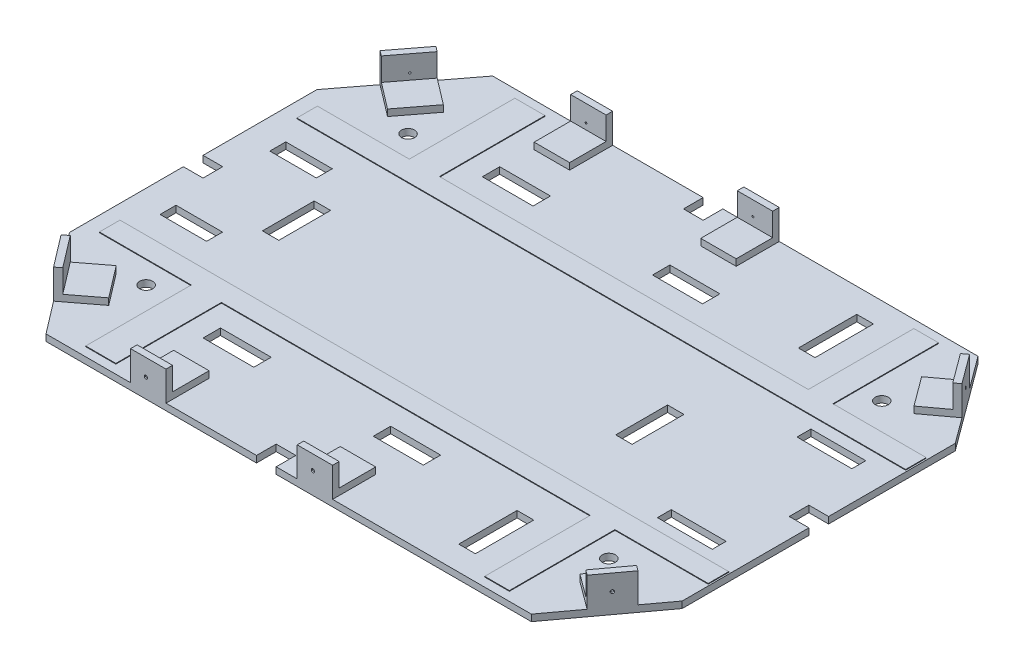
SolidWorks part; units mm, degrees
ref_plane "Front Plane" through (0, 0, 0) normal (0, 0, 1) x (1, 0, 0)
ref_plane "Top Plane" through (0, 0, 0) normal (0, 1, 0) x (1, 0, 0)
ref_plane "Right Plane" through (0, 0, 0) normal (1, 0, 0) x (0, 0, -1)
sketch "Sketch2" plane through (0, 0, 0) normal (0, 1, 0) x (1, 0, 0)
  line L0 (0, -190.295) -> (0, 190.295)
  line L1 (0, 190.295) -> (118.58, 345.4877)
  line L2 (118.58, 345.4877) -> (863.58, 345.4877)
  line L3 (863.58, 345.4877) -> (963.71, 209.8289)
  line L4 (963.71, 209.8289) -> (963.71, -209.8289)
  line L5 (-252.0448, 0) -> (1397.8872, 0) construction
  line L6 (863.58, -345.4877) -> (963.71, -209.8289)
  line L7 (118.58, -345.4877) -> (863.58, -345.4877)
  line L8 (0, -190.295) -> (118.58, -345.4877)
  point P10 (963.71, 0)
  point P13 (0, 0)
  dimension "D1" = 745
  dimension "D2" = 380.59
  dimension "D3" = 195.31
  dimension "D4" = 168.61
  dimension "D5" = 118.58
  dimension "D6" = 100.13
extrude "Boss-Extrude1" add sketch "Sketch2" along normal blind 10 contours L2 L3 L4 L6 L7 L8 L0 L1
sketch "Sketch3" plane through (0, 10, 0) normal (0, 1, 0) x (1, 0, 0)
  line L0 (-153.0587, 0) -> (1034.1611, 0) construction
  line L1 (13.2156, 0) -> (983.2156, 0) construction
  line L2 (0, -190.295) -> (0, 190.295) construction
  line L3 (28.177, 166.1961) -> (168.2416, 166.1961)
  line L4 (28.177, 166.1961) -> (28.177, 134.8384)
  line L5 (28.177, 134.8384) -> (956.3666, 134.8384)
  line L6 (956.3666, 166.1961) -> (956.3666, 134.8384)
  line L7 (168.2416, 327.1659) -> (214.233, 327.1659)
  line L8 (168.2416, 327.1659) -> (168.2416, 166.1961)
  line L10 (214.233, 327.1659) -> (214.233, 166.1961)
  line L11 (776.5822, 327.1659) -> (814.2115, 327.1659)
  line L12 (776.5822, 327.1659) -> (776.5822, 166.1961)
  line L14 (814.2115, 327.1659) -> (814.2115, 166.1961)
  line L15 (963.71, 209.8289) -> (963.71, -209.8289) construction
  line L16 (214.233, 166.1961) -> (776.5822, 166.1961)
  line L17 (814.2115, 166.1961) -> (956.3666, 166.1961)
  line L18 (28.177, -166.1961) -> (28.177, -134.8384)
  line L19 (776.5822, -327.1659) -> (814.2115, -327.1659)
  line L20 (956.3666, -166.1961) -> (956.3666, -134.8384)
  line L21 (814.2115, -166.1961) -> (956.3666, -166.1961)
  line L22 (814.2115, -327.1659) -> (814.2115, -166.1961)
  line L23 (776.5822, -327.1659) -> (776.5822, -166.1961)
  line L24 (28.177, -134.8384) -> (956.3666, -134.8384)
  line L25 (214.233, -166.1961) -> (776.5822, -166.1961)
  line L26 (214.233, -327.1659) -> (214.233, -166.1961)
  line L27 (168.2416, -327.1659) -> (214.233, -327.1659)
  line L28 (168.2416, -327.1659) -> (168.2416, -166.1961)
  line L29 (28.177, -166.1961) -> (168.2416, -166.1961)
  point P19 (168.2416, 246.681)
  dimension "D1" = 970
  dimension "D2" = 134.8384
  dimension "D3" = 31.3578
  dimension "D4" = 928.1897
  dimension "D5" = 160.9698
  dimension "D6" = 160.9698
  dimension "D7" = 28.177
  dimension "D8" = 168.2416
  dimension "D9" = 562.3491
  dimension "D10" = 45.9914
  dimension "D11" = 149.4985
extrude "Boss-Extrude3" add sketch "Sketch3" along normal blind 1
sketch "Sketch4" plane through (0, 10, 0) normal (0, 1, 0) x (1, 0, 0)
  line L0 (250, 345.4877) -> (250, 274.8292)
  line L1 (118.58, 345.4877) -> (863.58, 345.4877) construction
  line L2 (250, 274.8292) -> (304.0127, 274.8292)
  line L3 (304.0127, 274.8292) -> (304.0127, 345.4877)
  line L4 (504.0127, 345.4877) -> (504.0127, 274.8292)
  line L5 (504.0127, 274.8292) -> (558.0127, 274.8292)
  line L6 (558.0127, 274.8292) -> (558.0127, 345.4877)
  line L7 (42.7892, 246.2957) -> (94.438, 206.8318)
  line L8 (0, 190.295) -> (118.58, 345.4877) construction
  line L9 (94.438, 206.8318) -> (131.2894, 255.0615)
  line L10 (131.2894, 255.0615) -> (79.6406, 294.5254)
  line L11 (901.1953, 294.5254) -> (855.1137, 260.5125)
  line L12 (863.58, 345.4877) -> (963.71, 209.8289) construction
  line L13 (855.1137, 260.5125) -> (888.0112, 215.9421)
  line L14 (888.0112, 215.9421) -> (934.0928, 249.9551)
  line L15 (42.7892, 246.2957) -> (79.6406, 294.5254)
  line L16 (250, 345.4877) -> (304.0127, 345.4877)
  line L17 (504.0127, 345.4877) -> (558.0127, 345.4877)
  line L18 (901.1953, 294.5254) -> (934.0928, 249.9551)
  line L19 (0, -190.295) -> (0, 190.295) construction
  line L20 (963.71, 209.8289) -> (963.71, -209.8289) construction
  line L21 (0, 0) -> (1280.3425, 0) construction
  line L22 (558.0127, -274.8292) -> (558.0127, -345.4877)
  line L23 (42.7892, -246.2957) -> (94.438, -206.8318)
  line L24 (94.438, -206.8318) -> (131.2894, -255.0615)
  line L25 (131.2894, -255.0615) -> (79.6406, -294.5254)
  line L26 (42.7892, -246.2957) -> (79.6406, -294.5254)
  line L27 (901.1953, -294.5254) -> (855.1137, -260.5125)
  line L28 (855.1137, -260.5125) -> (888.0112, -215.9421)
  line L29 (888.0112, -215.9421) -> (934.0928, -249.9551)
  line L30 (901.1953, -294.5254) -> (934.0928, -249.9551)
  line L31 (504.0127, -345.4877) -> (504.0127, -274.8292)
  line L32 (504.0127, -345.4877) -> (558.0127, -345.4877)
  line L33 (504.0127, -274.8292) -> (558.0127, -274.8292)
  line L34 (250, -345.4877) -> (304.0127, -345.4877)
  line L35 (304.0127, -274.8292) -> (304.0127, -345.4877)
  line L36 (250, -274.8292) -> (304.0127, -274.8292)
  line L37 (250, -345.4877) -> (250, -274.8292)
  dimension "D1" = 60.6971
  dimension "D2" = 65
  dimension "D3" = 54.0127
  dimension "D4" = 54
  dimension "D5" = 70.6585
  dimension "D6" = 70.6585
  dimension "D9" = 90.4262
  dimension "D10" = 250
  dimension "D11" = 200
  dimension "D12" = 84.9752
  dimension "D13" = 50.9623
  dimension "D14" = 29.6172
extrude "Boss-Extrude4" add sketch "Sketch4" along normal blind 10
sketch "Sketch5" plane through (0, 0, 345.4877) normal (0, 0, 1) x (1, 0, 0)
  line L5 (250, 10) -> (304, 10)
  line L6 (250, 10) -> (250, 66.8169)
  line L7 (250, 66.8169) -> (304, 66.8169)
  line L8 (304, 10) -> (304, 66.8169)
  line L9 (504.0127, 10) -> (558.1343, 10)
  line L10 (504.0127, 10) -> (504.0127, 66.8169)
  line L11 (504.0127, 66.8169) -> (558.1343, 66.8169)
  line L12 (558.1343, 10) -> (558.1343, 66.8169)
  dimension "D1" = 54
  dimension "D2" = 54.1217
  dimension "D3" = 56.8169
  dimension "D4" = 56.8169
extrude "Boss-Extrude6" add sketch "Sketch5" against normal blind 3
sketch "Sketch6" plane through (0, 0, 345.4877) normal (0, 0, 1) x (1, 0, 0)
  line L0 (304, 20) -> (304, 66.8169) construction
  line L1 (558.1343, 10) -> (558.1343, 66.8169) construction
  line L3 (304, 66.8169) -> (250, 66.8169) construction
  line L4 (558.1343, 66.8169) -> (504.0127, 66.8169) construction
  circle A0 centre (277, 40.5736) radius 3
  circle A1 centre (531.1343, 40.5736) radius 3
  dimension "D3" = 6
  dimension "D4" = 6
  dimension "D1" = 27
  dimension "D2" = 27
  dimension "D5" = 26.2433
  dimension "D6" = 26.2433
extrude "Cut-Extrude1" cut sketch "Sketch6" against normal up to next (3 mm away)
mirror "Mirror3" about plane through (0, 0, 0) normal (0, 0, 1) of "Cut-Extrude1", "Boss-Extrude6"
sketch "Sketch7" plane through (724.0998, 0, 534.4593) normal (0.8046, 0, 0.5939) x (0.5939, 0, -0.8046)
  line L0 (298.2131, 10) -> (298.2131, 0)
  line L2 (298.2131, 10) -> (298.2131, 60.6267)
  line L3 (298.2131, 60.6267) -> (353.4397, 60.6267)
  line L4 (353.4397, 10) -> (353.4397, 60.6267)
  line L5 (234.8722, 0) -> (403.4822, 0) construction
  line L6 (298.2131, 0) -> (353.4397, 0)
  line L8 (353.4397, 0) -> (353.4397, 10)
  dimension "D1" = 55.2266
  dimension "D2" = 50.6267
  dimension "D3" = 10
extrude "Boss-Extrude7" add sketch "Sketch7" against normal blind 3
sketch "Sketch8" plane through (721.6861, 0, 532.6777) normal (-0.8046, 0, -0.5939) x (-0.5939, 0, 0.8046)
  line L2 (-298.2131, 60.6267) -> (-298.2131, 10) construction
  line L4 (-353.6096, 10) -> (-403.4822, 10) construction
  circle A0 centre (-325.2131, 37) radius 3
  dimension "D1" = 6
  dimension "D2" = 27
  dimension "D3" = 27
extrude "Cut-Extrude6" cut sketch "Sketch8" against normal blind 10 contours A0
sketch "Sketch9" plane through (-91.8039, 0, 70.1457) normal (-0.7946, 0, 0.6071) x (0.6071, 0, 0.7946)
  line L0 (151.2078, 0) -> (346.5178, 0) construction
  line L1 (221.6847, 0) -> (282.3818, 0)
  line L2 (221.6847, 0) -> (221.6847, 59.2555)
  line L3 (221.6847, 59.2555) -> (282.3818, 59.2555)
  line L4 (282.3818, 0) -> (282.3818, 59.2555)
  line L6 (221.6847, 20) -> (221.6847, 10) construction
  dimension "D1" = 0
  dimension "D2" = 0
  dimension "D3" = 59.2555
extrude "Boss-Extrude8" add sketch "Sketch9" against normal blind 3
sketch "Sketch10" plane through (-91.8039, 0, 70.1457) normal (-0.7946, 0, 0.6071) x (0.6071, 0, 0.7946)
  line L0 (282.3818, 59.2555) -> (282.3818, 10) construction
  line L1 (282.3818, 59.2555) -> (221.6847, 59.2555) construction
  circle A0 centre (255.3818, 38.7376) radius 3
  dimension "D1" = 6
  dimension "D2" = 27
  dimension "D3" = 20.5179
extrude "Cut-Extrude7" cut sketch "Sketch10" against normal blind 10
mirror "Mirror4" about plane through (0, 0, 0) normal (0, 0, 1) of "Cut-Extrude6", "Cut-Extrude7", "Boss-Extrude8", "Boss-Extrude7"
sketch "Sketch12" plane through (0, 10, 0) normal (0, 1, 0) x (1, 0, 0)
  line L0 (28.177, 134.8384) -> (956.3666, 134.8384) construction
  line L1 (246.2115, 226.1119) -> (323.5237, 226.1119)
  line L2 (246.2115, 226.1119) -> (246.2115, 199.6351)
  line L3 (246.2115, 199.6351) -> (323.5237, 199.6351)
  line L4 (323.5237, 226.1119) -> (323.5237, 199.6351)
  line L5 (505.6841, 226.1119) -> (581.9373, 226.1119)
  line L6 (505.6841, 226.1119) -> (505.6841, 199.6351)
  line L7 (505.6841, 199.6351) -> (581.9373, 199.6351)
  line L8 (581.9373, 226.1119) -> (581.9373, 199.6351)
  line L9 (713.2622, 303.4242) -> (738.68, 303.4242)
  line L10 (713.2622, 303.4242) -> (713.2622, 214.4621)
  line L11 (713.2622, 214.4621) -> (738.68, 214.4621)
  line L12 (738.68, 303.4242) -> (738.68, 214.4621)
  line L13 (829.7602, 95.846) -> (913.4269, 95.846)
  line L14 (829.7602, 95.846) -> (829.7602, 117.0275)
  line L15 (829.7602, 117.0275) -> (913.4269, 117.0275)
  line L16 (913.4269, 95.846) -> (913.4269, 117.0275)
  line L17 (50.2831, 95.846) -> (121.241, 95.846)
  line L18 (50.2831, 95.846) -> (50.2831, 71.4874)
  line L19 (50.2831, 71.4874) -> (121.241, 71.4874)
  line L20 (121.241, 95.846) -> (121.241, 71.4874)
  line L21 (963.71, 209.8289) -> (963.71, -209.8289) construction
  line L22 (814.2115, 166.1961) -> (814.2115, 327.1659) construction
  line L23 (956.3666, 166.1961) -> (814.2115, 166.1961) construction
  line L24 (776.5822, 166.1961) -> (214.233, 166.1961) construction
  line L25 (776.5822, 327.1659) -> (776.5822, 166.1961) construction
  line L26 (776.5822, 166.1961) -> (214.233, 166.1961) construction
  line L27 (168.2416, 166.1961) -> (28.177, 166.1961) construction
  line L28 (168.2416, 327.1659) -> (168.2416, 166.1961) construction
  line L29 (28.177, 134.8384) -> (956.3666, 134.8384) construction
  line L30 (0, -190.295) -> (0, 190.295) construction
  line L31 (558.1343, 345.4877) -> (863.58, 345.4877) construction
  line L32 (150, 35.4877) -> (175, 35.4877)
  line L33 (150, 35.4877) -> (150, -39.5123)
  line L34 (150, -39.5123) -> (175, -39.5123)
  line L35 (175, 35.4877) -> (175, -39.5123)
  line L36 (688.71, 35.4877) -> (713.71, 35.4877)
  line L37 (688.71, 35.4877) -> (688.71, -39.5123)
  line L38 (688.71, -39.5123) -> (713.71, -39.5123)
  line L39 (713.71, 35.4877) -> (713.71, -39.5123)
  line L40 (118.58, 345.4877) -> (250, 345.4877) construction
  circle A0 centre (132.8908, 199.6351) radius 10
  circle A1 centre (846.7053, 208.1077) radius 10
  dimension "D9" = 20
  dimension "D22" = 20
  dimension "D24" = 35.3509
  dimension "D1" = 70.9578
  dimension "D2" = 24.3587
  dimension "D3" = 77.3123
  dimension "D4" = 26.4768
  dimension "D5" = 76.2532
  dimension "D6" = 26.4768
  dimension "D7" = 88.9621
  dimension "D8" = 25.4177
  dimension "D10" = 17.8109
  dimension "D11" = 21.1814
  dimension "D12" = 83.6667
  dimension "D13" = 50.2831
  dimension "D14" = 32.4939
  dimension "D15" = 41.9115
  dimension "D16" = 48.266
  dimension "D17" = 37.9022
  dimension "D18" = 131.3249
  dimension "D19" = 33.439
  dimension "D20" = 182.1604
  dimension "D21" = 33.439
  dimension "D23" = 33.439
  dimension "D25" = 38.9923
  dimension "D26" = 50.2831
  dimension "D27" = 150
  dimension "D28" = 250
  dimension "D29" = 25
  dimension "D30" = 25
  dimension "D31" = 75
  dimension "D32" = 75
  dimension "D33" = 310
  dimension "D34" = 310
extrude "Cut-Extrude8" cut sketch "Sketch12" against normal up to surface (10 mm away) up to face at (486.4675, 0, 0)
mirror "Mirror5" about plane through (0, 0, 0) normal (0, 0, 1) of "Cut-Extrude8"
sketch "Sketch13" plane through (0, 10, 0) normal (0, 1, 0) x (1, 0, 0)
  line L0 (0, -190.295) -> (0, 190.295) construction
  line L1 (0, 10) -> (30, 10)
  line L2 (0, 10) -> (0, -10)
  line L3 (0, -10) -> (30, -10)
  line L4 (30, 10) -> (30, -10)
  line L5 (963.71, 209.8289) -> (963.71, -209.8289) construction
  line L6 (963.71, 10) -> (933.71, 10)
  line L7 (963.71, 10) -> (963.71, -10)
  line L8 (963.71, -10) -> (933.71, -10)
  line L9 (933.71, 10) -> (933.71, -10)
  line L10 (304.0127, -345.4877) -> (504.0127, -345.4877) construction
  line L11 (447, -345.4877) -> (467, -345.4877)
  line L12 (447, -345.4877) -> (447, -315.4877)
  line L13 (447, -315.4877) -> (467, -315.4877)
  line L14 (467, -345.4877) -> (467, -315.4877)
  line L15 (304.0127, 345.4877) -> (504.0127, 345.4877) construction
  line L16 (447, 345.4877) -> (467, 345.4877)
  line L17 (447, 345.4877) -> (447, 315.4877)
  line L18 (447, 315.4877) -> (467, 315.4877)
  line L19 (467, 345.4877) -> (467, 315.4877)
  line L20 (0, 0) -> (1110.5264, 0) construction
  point P26 (963.71, 0)
  dimension "D1" = 447
  dimension "D2" = 447
  dimension "D3" = 20
  dimension "D4" = 30
  dimension "D5" = 20
  dimension "D6" = 20
  dimension "D7" = 20
  dimension "D8" = 30
  dimension "D9" = 30
  dimension "D10" = 30
extrude "Cut-Extrude9" cut sketch "Sketch13" against normal through all
sketch "Sketch15" plane through (0, 10, 0) normal (0, 1, 0) x (1, 0, 0)
  line L0 (5, 188.6034) -> (5, 15)
  line L1 (5, 15) -> (35, 15)
  line L2 (35, 15) -> (35, -15)
  line L3 (35, -15) -> (5, -15)
  line L4 (5, -15) -> (5, -188.6034)
  line L5 (5, -188.6034) -> (121.0521, -340.4877)
  line L6 (121.0521, -340.4877) -> (442, -340.4877)
  line L7 (442, -340.4877) -> (442, -310.4877)
  line L8 (442, -310.4877) -> (472, -310.4877)
  line L9 (472, -310.4877) -> (472, -340.4877)
  line L10 (472, -340.4877) -> (861.056, -340.4877)
  line L11 (861.056, -340.4877) -> (958.71, -208.1835)
  line L12 (958.71, -208.1835) -> (958.71, -15)
  line L13 (958.71, -15) -> (928.71, -15)
  line L14 (928.71, -15) -> (928.71, 15)
  line L15 (928.71, 15) -> (958.71, 15)
  line L16 (958.71, 15) -> (958.71, 208.1835)
  line L17 (958.71, 208.1835) -> (861.056, 340.4877)
  line L18 (861.056, 340.4877) -> (472, 340.4877)
  line L19 (472, 340.4877) -> (472, 310.4877)
  line L20 (472, 310.4877) -> (442, 310.4877)
  line L21 (442, 310.4877) -> (442, 340.4877)
  line L22 (442, 340.4877) -> (121.0521, 340.4877)
  line L23 (121.0521, 340.4877) -> (5, 188.6034)
  line L24 (0, 10) -> (30, 10)
  line L25 (0, 190.295) -> (0, 10)
  line L26 (118.58, 345.4877) -> (0, 190.295)
  line L27 (447, 345.4877) -> (118.58, 345.4877)
  line L28 (447, 315.4877) -> (447, 345.4877)
  line L29 (467, 315.4877) -> (447, 315.4877)
  line L30 (467, 345.4877) -> (467, 315.4877)
  line L31 (863.58, 345.4877) -> (467, 345.4877)
  line L32 (963.71, 209.8289) -> (863.58, 345.4877)
  line L33 (963.71, 10) -> (963.71, 209.8289)
  line L34 (933.71, 10) -> (963.71, 10)
  line L35 (933.71, -10) -> (933.71, 10)
  line L36 (963.71, -10) -> (933.71, -10)
  line L37 (963.71, -209.8289) -> (963.71, -10)
  line L38 (863.58, -345.4877) -> (963.71, -209.8289)
  line L39 (467, -345.4877) -> (863.58, -345.4877)
  line L40 (467, -315.4877) -> (467, -345.4877)
  line L41 (447, -315.4877) -> (467, -315.4877)
  line L42 (447, -345.4877) -> (447, -315.4877)
  line L43 (118.58, -345.4877) -> (447, -345.4877)
  line L44 (0, -190.295) -> (118.58, -345.4877)
  line L45 (0, -10) -> (0, -190.295)
  line L46 (30, -10) -> (0, -10)
  line L47 (30, 10) -> (30, -10)
  line L48 (0, 10) -> (30, 10)
  line L49 (0, 190.295) -> (0, 10)
  line L50 (118.58, 345.4877) -> (0, 190.295)
  line L51 (447, 345.4877) -> (118.58, 345.4877)
  line L52 (447, 315.4877) -> (447, 345.4877)
  line L53 (467, 315.4877) -> (447, 315.4877)
  line L54 (467, 345.4877) -> (467, 315.4877)
  line L55 (863.58, 345.4877) -> (467, 345.4877)
  line L56 (963.71, 209.8289) -> (863.58, 345.4877)
  line L57 (963.71, 10) -> (963.71, 209.8289)
  line L58 (933.71, 10) -> (963.71, 10)
  line L59 (933.71, -10) -> (933.71, 10)
  line L60 (963.71, -10) -> (933.71, -10)
  line L61 (963.71, -209.8289) -> (963.71, -10)
  line L62 (863.58, -345.4877) -> (963.71, -209.8289)
  line L63 (467, -345.4877) -> (863.58, -345.4877)
  line L64 (467, -315.4877) -> (467, -345.4877)
  line L65 (447, -315.4877) -> (467, -315.4877)
  line L66 (447, -345.4877) -> (447, -315.4877)
  line L67 (118.58, -345.4877) -> (447, -345.4877)
  line L68 (0, -190.295) -> (118.58, -345.4877)
  line L69 (0, -10) -> (0, -190.295)
  line L70 (30, -10) -> (0, -10)
  line L71 (30, 10) -> (30, -10)
  dimension "D1" = 0
  dimension "D2" = 5
extrude "Cut-Extrude11" cut sketch "Sketch15" against normal blind 10 and the other way blind 70
sketch "Sketch16" plane through (0, 0, 340.4877) normal (0, 0, 1) x (1, 0, 0)
  line L0 (250, 10) -> (250, 55)
  line L1 (304.0127, 10) -> (304.0127, 55)
  line L2 (304.0127, 55) -> (250, 55)
  line L3 (250, 10) -> (304.0127, 10)
  line L4 (504.0127, 10) -> (504.0127, 55)
  line L5 (558.0127, 10) -> (558.0127, 55)
  line L6 (558.0127, 55) -> (504.0127, 55)
  line L7 (504.0127, 10) -> (558.0127, 10)
  dimension "D1" = 45
  dimension "D2" = 45
extrude "Boss-Extrude9" add sketch "Sketch16" against normal blind 10
sketch "Sketch18" plane through (-87.8309, 0, 67.1101) normal (-0.7946, 0, 0.6071) x (0.6071, 0, 0.7946)
  line L1 (282.3818, 10) -> (221.575, 10)
  line L2 (282.3818, 10) -> (282.3818, 55)
  line L3 (282.3818, 55) -> (221.575, 55)
  line L4 (221.575, 10) -> (221.575, 55)
  dimension "D1" = 45
  dimension "D2" = 60.8068
extrude "Boss-Extrude10" add sketch "Sketch18" against normal blind 10
hole_wizard "CSK for #3 Flat Head Machine Screw (100)2" positions "3DSketch2" profile "Sketch19" countersink size "#3" standard "ANSI Inch" end condition up to next
sketch3d "3DSketch2"
  point P0 (65.5183, 29.7676, 267.8074)
sketch "Sketch19" plane through (65.5183, 29.7676, 267.8074) normal (0, 1, 0) x (0.6071, 0, 0.7946)
  line L0 (0, 0) -> (0, 10)
  line L1 (0, 10) -> (1.397, 10)
  line L2 (1.397, 10) -> (1.397, 0.9484)
  line L3 (1.397, 0.9484) -> (2.5273, 0)
  line L5 (2.5273, 0) -> (0, 0)
  line L6 (-1.397, 0.9484) -> (-2.5273, 0) construction
  line L11 (0, -6.35) -> (0, 107.95) construction
  dimension "Thru Hole Dia." = 2.794
  dimension "Thru Hole Depth" = 10
  dimension "Near C'Sink Dia." = 5.0546
  dimension "Near C'Sink Angle" = 100
sketch "Sketch20" plane through (720.0769, 0, 531.49) normal (0.8046, 0, 0.5939) x (0.5939, 0, -0.8046)
  line L0 (298.2131, 10) -> (298.2131, 55)
  line L1 (353.6096, 10) -> (353.6096, 55)
  line L2 (353.6096, 55) -> (298.2131, 55)
  line L3 (298.2131, 10) -> (353.6096, 10)
  dimension "D1" = 45
extrude "Boss-Extrude11" add sketch "Sketch20" against normal blind 10
hole_wizard "CSK for #3 Flat Head Machine Screw (100)3" positions "3DSketch3" profile "Sketch21" countersink size "#3" standard "ANSI Inch" end condition up to next
sketch3d "3DSketch3"
  point P0 (913.5252, 30.4081, 269.4011)
sketch "Sketch21" plane through (913.5252, 30.4081, 269.4011) normal (0, 1, 0) x (0.5939, 0, -0.8046)
  line L0 (0, 0) -> (0, 10)
  line L1 (0, 10) -> (1.397, 10)
  line L2 (1.397, 10) -> (1.397, 0.9484)
  line L3 (1.397, 0.9484) -> (2.5273, 0)
  line L5 (2.5273, 0) -> (0, 0)
  line L6 (-1.397, 0.9484) -> (-2.5273, 0) construction
  line L11 (0, -6.35) -> (0, 107.95) construction
  dimension "Thru Hole Dia." = 2.794
  dimension "Thru Hole Depth" = 10
  dimension "Near C'Sink Dia." = 5.0546
  dimension "Near C'Sink Angle" = 100
hole_wizard "CSK for #3 Flat Head Machine Screw (100)4" positions "3DSketch5" profile "Sketch23" countersink size "#3" standard "ANSI Inch" end condition up to next
sketch3d "3DSketch5"
  point P0 (273.4188, 29.044, 340.4877)
  point P2 (528.0133, 32.812, 340.4877)
sketch "Sketch23" plane through (273.4188, 29.044, 340.4877) normal (1, 0, 0) x (0, -1, 0)
  line L0 (0, 0) -> (0, 10)
  line L1 (0, 10) -> (1.397, 10)
  line L2 (1.397, 10) -> (1.397, 0.9484)
  line L3 (1.397, 0.9484) -> (2.5273, 0)
  line L5 (2.5273, 0) -> (0, 0)
  line L6 (-1.397, 0.9484) -> (-2.5273, 0) construction
  line L11 (0, -6.35) -> (0, 107.95) construction
  dimension "Thru Hole Dia." = 2.794
  dimension "Thru Hole Depth" = 10
  dimension "Near C'Sink Dia." = 5.0546
  dimension "Near C'Sink Angle" = 100
mirror "Mirror7" about plane through (0, 0, 0) normal (0, 0, 1) of "Boss-Extrude10", "CSK for #3 Flat Head Machine Screw (100)2", "Boss-Extrude11", "CSK for #3 Flat Head Machine Screw (100)3", "CSK for #3 Flat Head Machine Screw (100)4", "Boss-Extrude9"
equation "\"D6@Sketch6\"=\"D5@Sketch6\""
